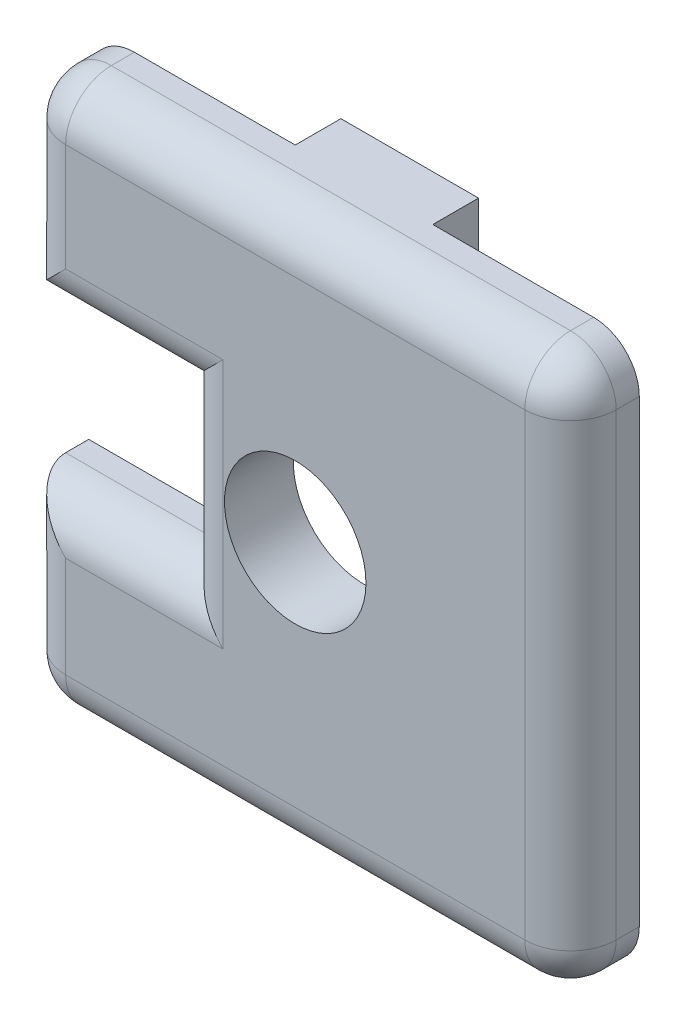
SolidWorks part; units mm, degrees
ref_plane "Front Plane" through (0, 0, 0) normal (0, 0, 1) x (1, 0, 0)
ref_plane "Top Plane" through (0, 0, 0) normal (0, 1, 0) x (1, 0, 0)
ref_plane "Right Plane" through (0, 0, 0) normal (1, 0, 0) x (0, 0, -1)
sketch "Sketch1" plane through (0, 0, 0) normal (0, 0, 1) x (1, 0, 0)
  line L0 (-5.4416, 0) -> (12.7, 0) construction
  line L1 (-12.7, 12.7) -> (12.7, 12.7)
  line L2 (-12.7, 12.7) -> (-12.7, 3.5208)
  line L3 (-12.7, -12.7) -> (12.7, -12.7)
  line L4 (12.7, 12.7) -> (12.7, -12.7)
  line L5 (0, 12.7) -> (0, -12.7) construction
  line L6 (-12.7, -3.8221) -> (-12.7, -12.7)
  line L7 (-12.7, 3.5208) -> (-5.4416, 3.5208)
  line L9 (-12.7, -3.8221) -> (-5.4416, -3.8221)
  line L10 (-5.4416, 3.5208) -> (-5.4416, -3.8221)
  dimension "D1" = 25.4
  dimension "D2" = 25.4
extrude "Boss-Extrude1" add sketch "Sketch1" along normal blind 3.175
fillet "Fillet1" radius 2.1082 12 edges at (0, 12.7, 3.175) (12.7, 0, 3.175) (0, -12.7, 3.175) (-12.7, 8.1104, 3.175) (12.7, -12.7, 1.5875) (12.7, 12.7, 1.5875) (-12.7, 12.7, 1.5875) (-12.7, -8.261, 3.175) (-9.0708, -3.8221, 3.175) (-5.4416, -0.1506, 3.175) (-9.0708, 3.5208, 3.175) (-12.7, -12.7, 1.5875)
sketch "Sketch2" plane through (0, 0, 3.175) normal (0, 0, 1) x (1, 0, 0)
  circle A0 centre (0, 0) radius 3.2639
  dimension "D2" = 6.5278
extrude "Cut-Extrude1" cut sketch "Sketch2" against normal up to next
sketch "Sketch3" plane through (0, 0, 0) normal (0, 0, -1) x (-1, 0, 0)
  line L0 (-10.5918, 12.7) -> (10.5918, 12.7) construction
  line L1 (-3.175, 12.7) -> (3.175, 12.7)
  line L2 (-3.175, 12.7) -> (-3.175, 10.5918)
  line L3 (-3.175, 10.5918) -> (3.175, 10.5918)
  line L4 (3.175, 12.7) -> (3.175, 10.5918)
  line L5 (0, 0) -> (0, 12.7) construction
  dimension "D1" = 6.35
  dimension "D2" = 2.1082
extrude "Boss-Extrude2" add sketch "Sketch3" along normal blind 2.1082
